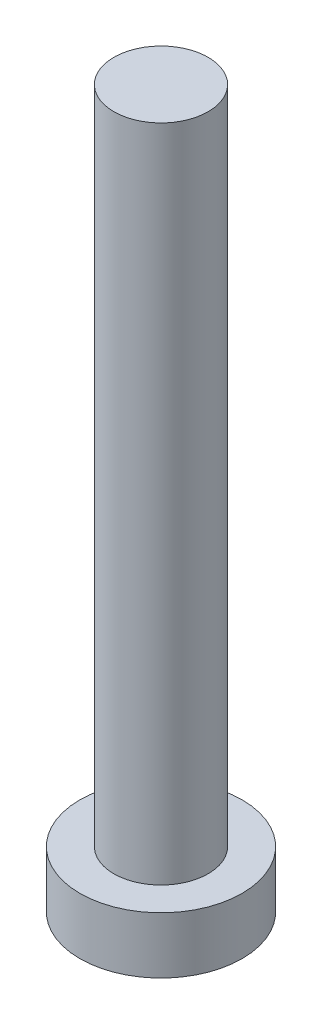
SolidWorks part; units mm, degrees
ref_plane "前视基准面" through (0, 0, 0) normal (0, 0, 1) x (1, 0, 0)
ref_plane "上视基准面" through (0, 0, 0) normal (0, 1, 0) x (1, 0, 0)
ref_plane "右视基准面" through (0, 0, 0) normal (1, 0, 0) x (0, 0, -1)
sketch "草图1" plane through (0, 0, 0) normal (0, 1, 0) x (1, 0, 0)
  circle A0 centre (0, 0) radius 4.3
extrude "凸台-拉伸1" add sketch "草图1" along normal blind 3
sketch "草图2" plane through (0, 3, 0) normal (0, 1, 0) x (1, 0, 0)
  circle A0 centre (0, 0) radius 2.5
extrude "凸台-拉伸2" add sketch "草图2" along normal blind 35
sketch "草图3" plane through (0, 0, 0) normal (0, -1, 0) x (1, 0, 0)
  line L0 (-0.6, 1.1) -> (-0.6, 2.4)
  line L1 (-2.4, -0.6) -> (-1.1, -0.6)
  line L2 (-2.4, -0.6) -> (-2.4, 0.6)
  line L3 (-2.4, 0.6) -> (-1.1, 0.6)
  line L4 (2.4, -0.6) -> (2.4, 0.6)
  line L5 (-2.4, -0.6) -> (2.4, 0.6) construction
  line L6 (-2.4, 0.6) -> (2.4, -0.6) construction
  line L7 (-0.6, -2.4) -> (0.6, -2.4)
  line L8 (-0.6, -2.4) -> (-0.6, -1.1)
  line L9 (-0.6, 2.4) -> (0.6, 2.4)
  line L10 (0.6, -2.4) -> (0.6, -1.1)
  line L11 (-0.6, -2.4) -> (0.6, 2.4) construction
  line L12 (-0.6, 2.4) -> (0.6, -2.4) construction
  line L13 (1.1, -0.6) -> (2.4, -0.6)
  line L14 (0.6, 1.1) -> (0.6, 2.4)
  line L15 (1.1, 0.6) -> (2.4, 0.6)
  arc A0 (-0.6, -1.1) -> (-1.1, -0.6) centre (-1.1, -1.1) ccw
  arc A1 (1.1, -0.6) -> (0.6, -1.1) centre (1.1, -1.1) ccw
  arc A2 (0.6, 1.1) -> (1.1, 0.6) centre (1.1, 1.1) ccw
  arc A3 (-0.6, 1.1) -> (-1.1, 0.6) centre (-1.1, 1.1) cw
  point P0 (0, 0)
  point P6 (0, 0)
  point P21 (0.6, 0.6)
  dimension "D1" = 0.5
extrude "切除-拉伸1" cut sketch "草图3" against normal blind 1.5
